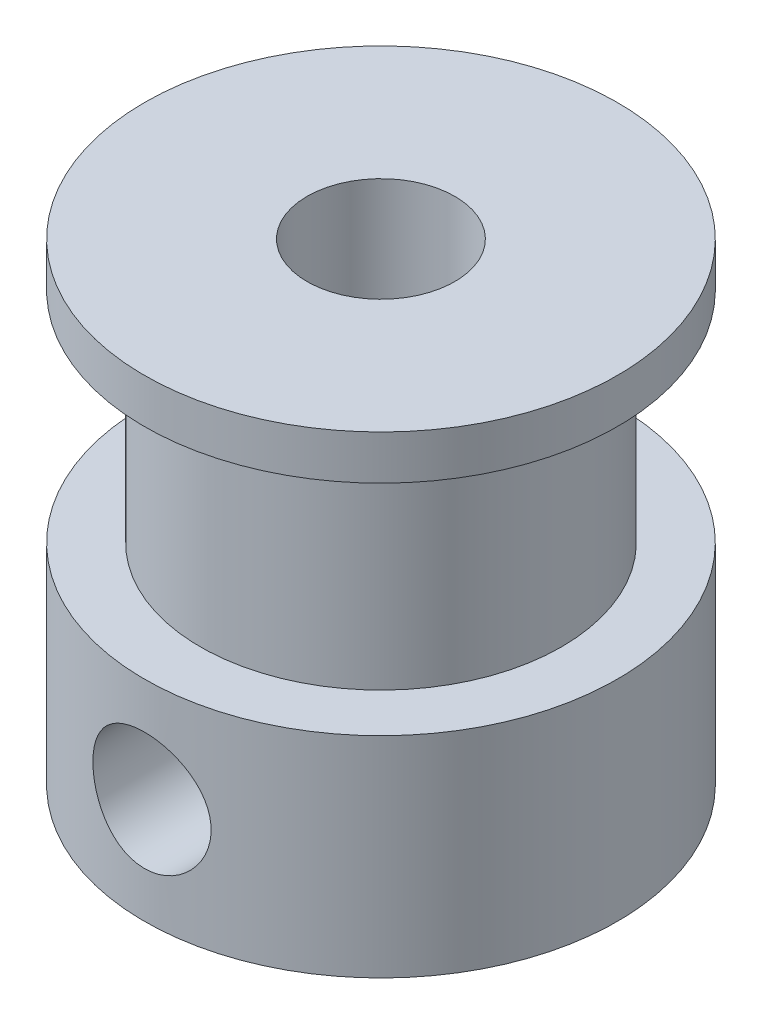
SolidWorks part; units mm, degrees
material "1060 Alloy"
ref_plane "Front Plane" through (0, 0, 0) normal (0, 0, 1) x (1, 0, 0)
ref_plane "Top Plane" through (0, 0, 0) normal (0, 1, 0) x (1, 0, 0)
ref_plane "Right Plane" through (0, 0, 0) normal (1, 0, 0) x (0, 0, -1)
sketch "Sketch1" plane through (0, 0, 0) normal (0, 0, 1) x (1, 0, 0)
  line L0 (0, 0) -> (0, 16)
  line L1 (0, 16) -> (-5.5, 16)
  line L2 (-5.5, 16) -> (-5.5, 14.5)
  line L3 (-5.5, 14.5) -> (-3.61, 14.5)
  line L4 (-3.61, 14.5) -> (-3.61, 7.1)
  line L5 (0, 0) -> (-5.5, 0)
  line L6 (-5.5, 0) -> (-5.5, 7.1)
  line L7 (-5.5, 7.1) -> (-3.61, 7.1)
  line L8 (2.5, 19.4948) -> (2.5, -3.2354) construction
  dimension "D1" = 16
  dimension "D2" = 5.5
  dimension "D3" = 2.5
  dimension "D4" = 7.4
  dimension "D5" = 7.1
  dimension "D6" = 6.11
revolve "Revolve1" add sketch "Sketch1" angle 360 about L8
sketch "Sketch2" plane through (0, 0, 0) normal (0, 0, 1) x (1, 0, 0)
  line L0 (-5.5, 3.55) -> (10.5, 3.55) construction
  line L1 (-5.5, 7.1) -> (-5.5, 0) construction
  line L2 (10.5, 0) -> (10.5, 7.1) construction
  circle A0 centre (2.5, 3.55) radius 2
  point P8 (2.5, 3.55)
  dimension "4" = 4
extrude "Cut-Extrude1" cut sketch "Sketch2" along normal blind 10
